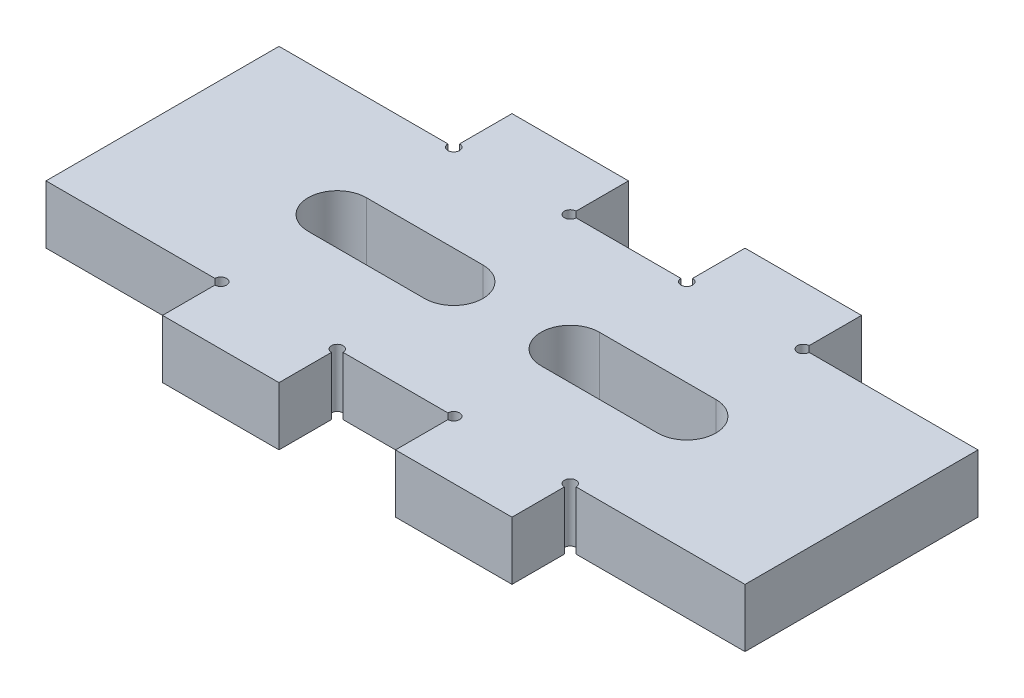
SolidWorks part; units mm, degrees
material "Acrylic (Medium-high impact)"
ref_plane "Front Plane" through (0, 0, 0) normal (0, 0, 1) x (1, 0, 0)
ref_plane "Top Plane" through (0, 0, 0) normal (0, 1, 0) x (1, 0, 0)
ref_plane "Right Plane" through (0, 0, 0) normal (1, 0, 0) x (0, 0, -1)
sketch "Sketch1" plane through (0, 0, 0) normal (0, 1, 0) x (1, 0, 0)
  line L0 (-19.05, 12.7) -> (-19.05, 19.05)
  line L1 (-38.1, 12.7) -> (-19.05, 12.7)
  line L2 (-38.1, 12.7) -> (-38.1, -12.7)
  line L3 (-38.1, -12.7) -> (-19.05, -12.7)
  line L4 (38.1, 12.7) -> (38.1, -12.7)
  line L5 (-38.1, 12.7) -> (38.1, -12.7) construction
  line L6 (-38.1, -12.7) -> (38.1, 12.7) construction
  line L7 (-19.05, 19.05) -> (-6.35, 19.05)
  line L8 (-6.35, 19.05) -> (-6.35, 12.7)
  line L9 (-6.35, 12.7) -> (6.35, 12.7)
  line L10 (0, -4.7893) -> (0, 19.05) construction
  line L11 (6.35, 19.05) -> (6.35, 12.7)
  line L12 (19.05, 19.05) -> (6.35, 19.05)
  line L13 (19.05, 12.7) -> (19.05, 19.05)
  line L14 (-8.6907, 0) -> (8.2657, 0) construction
  line L15 (-6.35, -19.05) -> (-6.35, -12.7)
  line L16 (-19.05, -19.05) -> (-6.35, -19.05)
  line L17 (-19.05, -12.7) -> (-19.05, -19.05)
  line L18 (19.05, -12.7) -> (19.05, -19.05)
  line L19 (19.05, -19.05) -> (6.35, -19.05)
  line L20 (6.35, -19.05) -> (6.35, -12.7)
  line L21 (19.05, 12.7) -> (38.1, 12.7)
  line L22 (19.05, -12.7) -> (38.1, -12.7)
  line L23 (-6.35, -12.7) -> (6.35, -12.7)
  point P0 (0, 0)
  dimension "D1" = 25.4
  dimension "D2" = 6.35
  dimension "D3" = 12.7
  dimension "D4" = 12.7
  dimension "D5" = 19.05
extrude "Boss-Extrude1" add sketch "Sketch1" along normal blind 6.35
sketch "Sketch2" plane through (0, 6.35, 0) normal (0, 1, 0) x (1, 0, 0)
  line L0 (-6.35, 19.05) -> (-19.05, 19.05) construction
  line L1 (19.05, 19.05) -> (6.35, 19.05) construction
  circle A0 centre (-12.7, 0) radius 3.175
  circle A1 centre (12.7, 0) radius 3.175
  point P7 (-12.7, 19.05)
  point P10 (12.7, 19.05)
  dimension "D1" = 6.35
  dimension "D2" = 6.35
extrude "Cut-Extrude1" cut sketch "Sketch2" against normal up to next
sketch "Sketch3" plane through (0, 6.35, 0) normal (0, 1, 0) x (1, 0, 0)
  point P0 (-19.05, 12.7)
  point P1 (-6.35, 12.7)
  point P3 (6.35, 12.7)
  point P5 (19.05, 12.7)
  point P7 (19.05, -12.7)
  point P9 (6.35, -12.7)
  point P11 (-6.35, -12.7)
  point P13 (-19.05, -12.7)
sketch "Sketch4" plane through (0, 6.35, 0) normal (0, 1, 0) x (1, 0, 0)
  circle A0 centre (-19.05, 12.7) radius 0.635
  dimension "D1" = 1.27
extrude "Cut-Extrude2" cut sketch "Sketch4" against normal up to next
pattern_sketch "Sketch-Pattern1" of "Cut-Extrude2" driven by "Sketch3"
sketch "Sketch5" plane through (0, 6.35, 0) normal (0, 1, 0) x (1, 0, 0)
  line L0 (-19.05, 0) -> (-6.35, 0) construction
  line L1 (-19.05, 3.175) -> (-6.35, 3.175)
  line L2 (-19.05, -3.175) -> (-6.35, -3.175)
  line L3 (0, -3.175) -> (0, 3.6826) construction
  line L4 (19.05, 0) -> (6.35, 0) construction
  line L5 (19.05, 3.175) -> (6.35, 3.175)
  line L6 (19.05, -3.175) -> (6.35, -3.175)
  arc A0 (-19.05, 3.175) -> (-19.05, -3.175) centre (-19.05, 0) ccw
  arc A1 (-6.35, -3.175) -> (-6.35, 3.175) centre (-6.35, 0) ccw
  circle A2 centre (-12.7, 0) radius 3.175 construction
  arc A3 (19.05, 3.175) -> (19.05, -3.175) centre (19.05, 0) cw
  arc A4 (6.35, -3.175) -> (6.35, 3.175) centre (6.35, 0) cw
  point P3 (-12.7, 0)
  point P14 (12.7, 0)
  dimension "D1" = 6.35
extrude "Cut-Extrude3" cut sketch "Sketch5" against normal up to next
